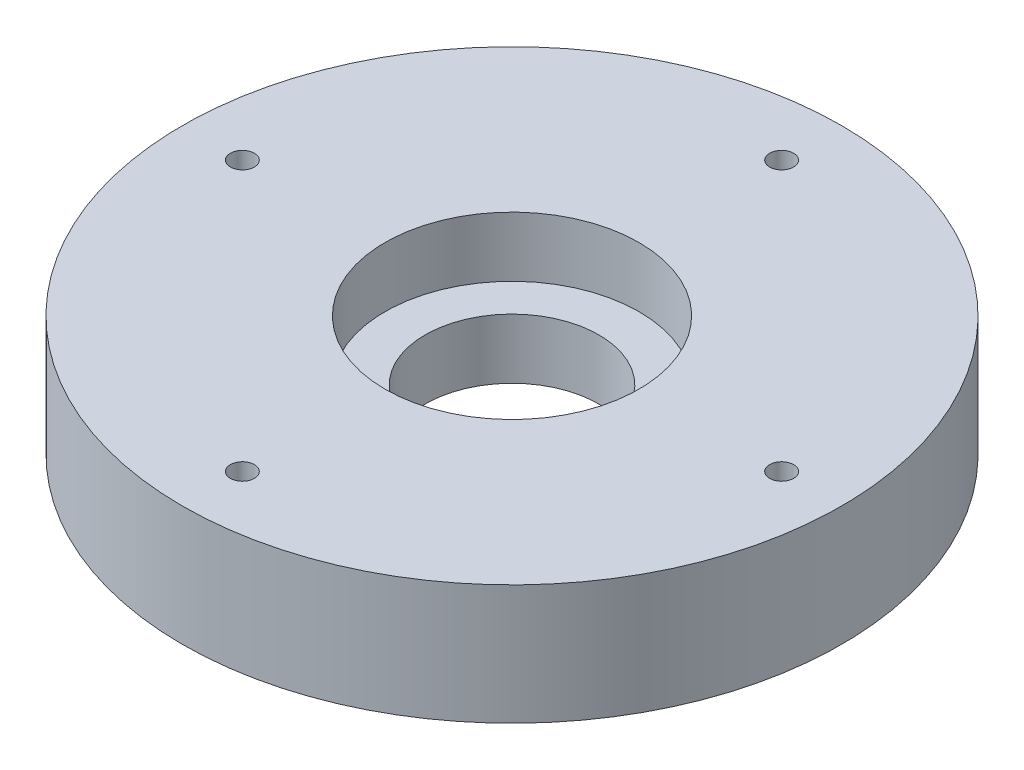
SolidWorks part; units mm, degrees
material "ABS"
ref_plane "Front Plane" through (0, 0, 0) normal (0, 0, 1) x (1, 0, 0)
ref_plane "Top Plane" through (0, 0, 0) normal (0, 1, 0) x (1, 0, 0)
ref_plane "Right Plane" through (0, 0, 0) normal (1, 0, 0) x (0, 0, -1)
sketch "Sketch1" plane through (0, 0, 0) normal (0, 1, 0) x (1, 0, 0)
  circle A0 centre (0, 0) radius 55
  circle A1 centre (0, 0) radius 14.5
  dimension "D1" = 110
  dimension "D2" = 29
extrude "Boss-Extrude1" add sketch "Sketch1" along normal blind 20
sketch "Sketch2" plane through (0, 20, 0) normal (0, 1, 0) x (1, 0, 0)
  circle A0 centre (0, 0) radius 21.2
  dimension "D1" = 42.4
extrude "Cut-Extrude1" cut sketch "Sketch2" against normal blind 10
sketch "Sketch4" plane through (0, 20, 0) normal (0, 1, 0) x (1, 0, 0)
  line L0 (0, 0) -> (42.5992, 0) construction
  line L1 (0, 0) -> (0, 40.5872) construction
  circle A0 centre (0, 45) radius 2
  circle A1 centre (45, 0) radius 2
  circle A2 centre (0, -45) radius 2
  circle A3 centre (-45, 0) radius 2
  point P15 (0, 0)
  dimension "D1" = 4
  dimension "D2" = 45
  dimension "D3" = 4
extrude "Cut-Extrude2" cut sketch "Sketch4" against normal blind 20
sketch "Sketch6" plane through (0, 0, 0) normal (0, -1, 0) x (1, 0, 0)
  circle A0 centre (0, 45) radius 5
  circle A1 centre (45, 0) radius 5
  circle A2 centre (0, -45) radius 5
  circle A3 centre (-45, 0) radius 5
  point P12 (0, 0)
  dimension "D1" = 10
  dimension "D2" = 4
extrude "Cut-Extrude3" cut sketch "Sketch6" against normal blind 5
